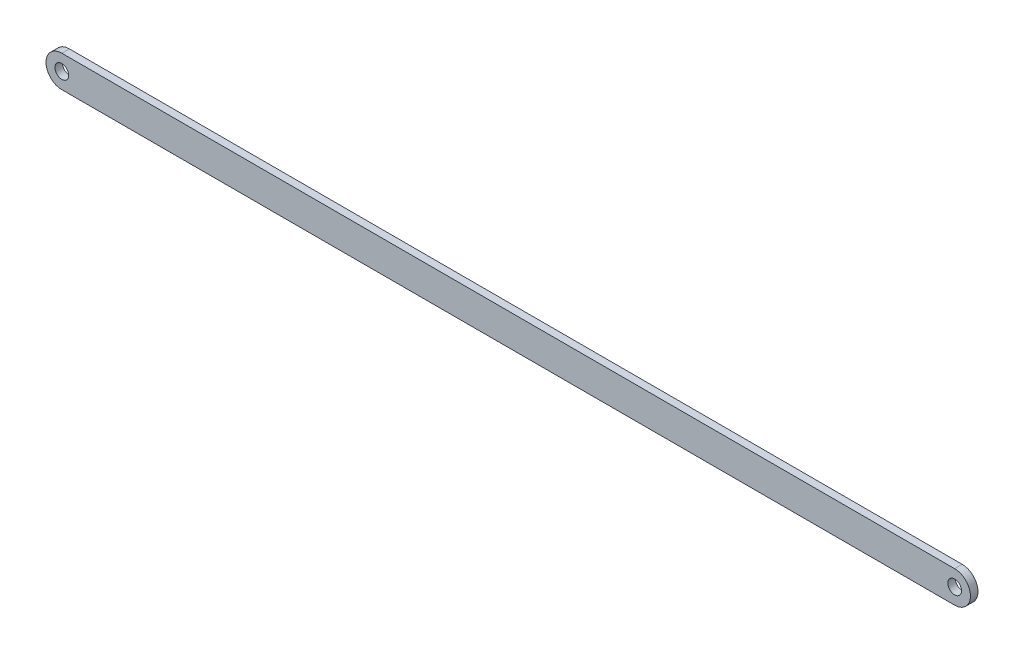
SolidWorks part; units mm, degrees
material "1.0490 (S275N)"
ref_plane "Front Plane" through (0, 0, 0) normal (0, 0, 1) x (1, 0, 0)
ref_plane "Top Plane" through (0, 0, 0) normal (0, 1, 0) x (1, 0, 0)
ref_plane "Right Plane" through (0, 0, 0) normal (1, 0, 0) x (0, 0, -1)
sketch "Sketch1" plane through (0, 0, 0) normal (0, 0, 1) x (1, 0, 0)
  line L0 (-325, 0) -> (325, 0) construction
  line L1 (-325, 11.5) -> (325, 11.5)
  line L2 (-325, -11.5) -> (325, -11.5)
  arc A0 (-325, 11.5) -> (-325, -11.5) centre (-325, 0) ccw
  arc A1 (325, -11.5) -> (325, 11.5) centre (325, 0) ccw
  circle A2 centre (-325, 0) radius 5
  circle A3 centre (325, 0) radius 5
  point P3 (0, 0)
  dimension "D3" = 10
  dimension "D4" = 10
  dimension "D1" = 650
  dimension "D2" = 23
  dimension "D5" = 325
extrude "Boss-Extrude1" add sketch "Sketch1" along normal mid plane 5.5
